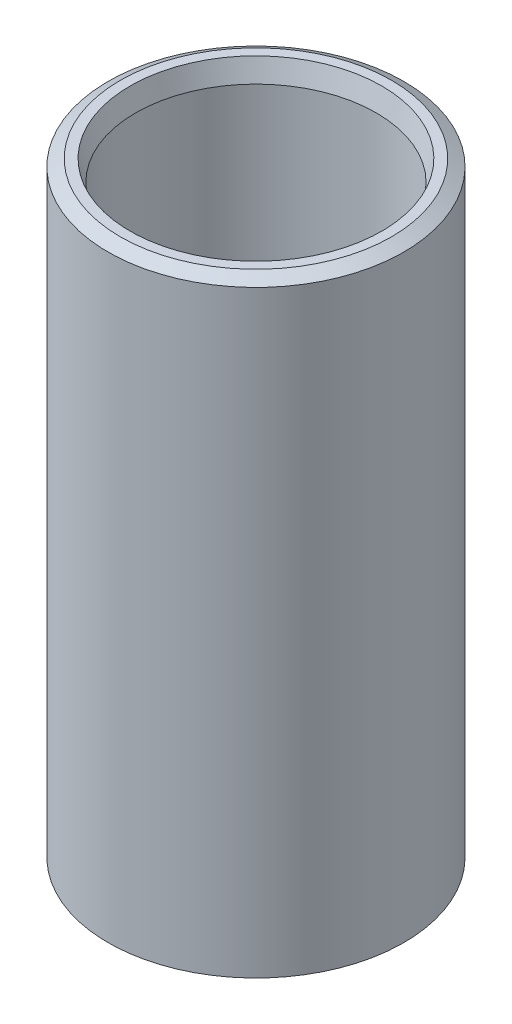
SolidWorks part; units mm, degrees
ref_plane "Ebene vorne" through (0, 0, 0) normal (0, 0, 1) x (1, 0, 0)
ref_plane "Ebene oben" through (0, 0, 0) normal (0, 1, 0) x (1, 0, 0)
ref_plane "Ebene rechts" through (0, 0, 0) normal (1, 0, 0) x (0, 0, -1)
sketch "Durchmesser/ WD" plane through (0, 0, 0) normal (0, 1, 0) x (1, 0, 0)
  circle A0 centre (0, 0) radius 24.15
  circle A1 centre (0, 0) radius 19.65
  dimension "da" = 48.3
  dimension "s" = 4.5
extrude "Rohr" add sketch "Durchmesser/ WD" along normal blind 100
sketch "Achse" plane through (0, 0, 0) normal (0, 0, 1) x (1, 0, 0)
  line L0 (0, 0) -> (0, 100) construction
  line L1 (19.65, 100) -> (-19.65, 100) construction
sketch "Fase1" plane through (0, 0, 0) normal (0, 0, 1) x (1, 0, 0)
  line L0 (24.15, 100) -> (19.65, 100)
  line L1 (-53.55, 100) -> (-57.15, 100)
  line L2 (24.15, 100) -> (-24.15, 100) construction
  line L3 (24.15, 100) -> (19.65, 100) construction
  line L4 (24.15, 100) -> (24.15, 98.8453)
  line L5 (24.15, 98.8453) -> (22.15, 100)
  line L6 (22.15, 100) -> (24.15, 100)
  line L7 (0, 0) -> (0, 50000) construction
  line L8 (20.55, 100) -> (19.65, 100)
  line L9 (19.65, 100) -> (19.65, 96.6412)
  line L10 (19.65, 96.6412) -> (20.55, 100)
  point P9 (20.55, 100)
  dimension "D1" = 30
  dimension "Anschluss1" = 3.6
  dimension "D3" = 1.6
  dimension "D4" = 15
sketch "Fase2" plane through (0, 0, 0) normal (0, 0, 1) x (1, 0, 0)
  line L0 (24.15, 0) -> (19.65, 0)
  line L1 (-53.55, 0) -> (-57.15, 0)
  line L2 (24.15, 0) -> (24.15, 1.1547)
  line L3 (24.15, 0) -> (19.65, 0) construction
  line L4 (24.15, 1.1547) -> (22.15, 0)
  line L5 (22.15, 0) -> (24.15, 0)
  line L6 (20.55, 0) -> (19.65, 0)
  line L7 (19.65, 0) -> (19.65, 3.3588)
  line L8 (19.65, 3.3588) -> (20.55, 0)
  point P4 (20.55, 0)
  dimension "D1" = 30
  dimension "D2" = 1.6
  dimension "D3" = 3.6
  dimension "Anschluss2" = 15
revolve "Schweißfase 1" cut sketch "Fase1" angle 360 about L7
revolve "Schweißfase 2" cut sketch "Fase2" angle 360 about L0
other "PropertyManager"
